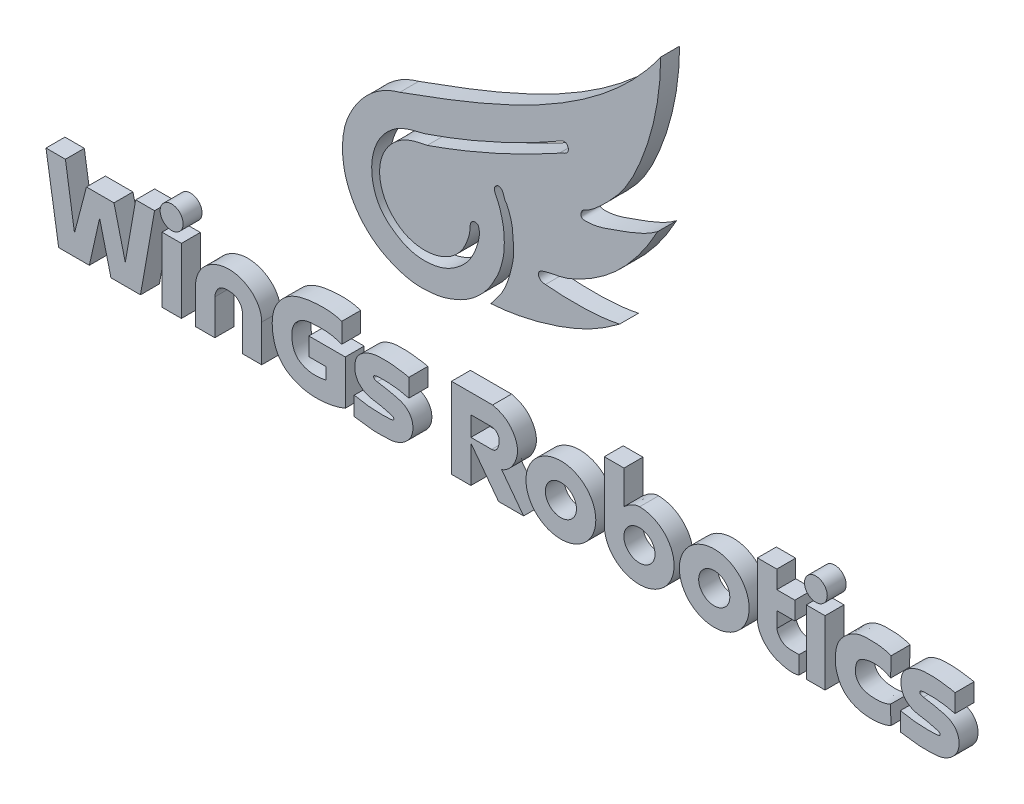
SolidWorks part; units mm, degrees
ref_plane "前视基准面" through (0, 0, 0) normal (0, 0, 1) x (1, 0, 0)
ref_plane "上视基准面" through (0, 0, 0) normal (0, 1, 0) x (1, 0, 0)
ref_plane "右视基准面" through (0, 0, 0) normal (1, 0, 0) x (0, 0, -1)
other "Configuration Table"
sketch "Sketch1" plane through (0, 0, 0) normal (0, 0, 1) x (1, 0, 0)
  line L1 (0, 0) -> (116, 0)
  line L2 (0, 0) -> (0, 86)
  line L3 (0, 86) -> (116, 86)
  line L4 (116, 0) -> (116, 86)
  dimension "D1" = 116
  dimension "D2" = 86
extrude "Boss-Extrude1" add sketch "Sketch1" along normal blind 2
sketch "Sketch2" plane through (0, 0, 2) normal (0, 0, 1) x (1, 0, 0)
  line L0 (9.8027, 28.235) -> (11.8527, 28.235)
  line L1 (11.8527, 28.235) -> (12.8123, 21.9684)
  line L2 (12.8123, 21.9684) -> (14.0773, 26.8101)
  line L3 (14.0773, 26.8101) -> (16.9852, 26.8101)
  line L4 (16.9852, 26.8101) -> (18.1775, 21.9684)
  line L5 (18.1775, 21.9684) -> (19.2825, 28.235)
  line L6 (19.2825, 28.235) -> (21.2744, 28.235)
  line L7 (21.2744, 28.235) -> (19.7853, 19.7903)
  line L8 (19.7853, 19.7903) -> (16.6653, 19.7903)
  line L9 (16.6653, 19.7903) -> (15.4678, 24.6536)
  line L10 (15.4678, 24.6536) -> (14.3826, 19.7903)
  line L11 (14.3826, 19.7903) -> (11.1403, 19.7903)
  line L12 (11.1403, 19.7903) -> (9.8027, 28.235)
  line L13 (22.0595, 26.6647) -> (24.1096, 26.6647)
  line L14 (24.1096, 26.6647) -> (24.1096, 19.7903)
  line L15 (24.1096, 19.7903) -> (22.0595, 19.7903)
  line L16 (22.0595, 19.7903) -> (22.0595, 26.6647)
  line L17 (32.5933, 23.6986) -> (32.5933, 19.7903)
  line L18 (32.5933, 19.7903) -> (30.5505, 19.7903)
  line L19 (30.5505, 19.7903) -> (30.5505, 23.5343)
  line L20 (27.6427, 23.5343) -> (27.6427, 19.7903)
  line L21 (27.6427, 19.7903) -> (25.5972, 19.7903)
  line L22 (25.5972, 19.7903) -> (25.5972, 23.6986)
  line L23 (41.4245, 20.2317) -> (41.4245, 24.9256)
  line L24 (41.4245, 24.9256) -> (37.5759, 24.9256)
  line L25 (37.5759, 24.9256) -> (37.5759, 23.026)
  line L26 (37.5759, 23.026) -> (39.3929, 23.026)
  line L27 (39.3929, 23.026) -> (39.3929, 21.7872)
  line L28 (41.0585, 28.009) -> (41.0585, 25.9029)
  line L29 (42.3726, 19.9426) -> (42.3726, 21.9041)
  line L30 (48.1482, 26.4281) -> (48.1482, 24.5174)
  line L31 (57.9509, 22.8769) -> (60.2681, 19.7995)
  line L32 (60.2681, 19.7995) -> (57.6234, 19.7995)
  line L33 (57.6234, 19.7995) -> (54.6991, 23.6831)
  line L34 (54.6991, 23.6831) -> (54.6991, 19.7995)
  line L35 (54.6991, 19.7995) -> (52.65, 19.7995)
  line L36 (52.65, 19.7995) -> (52.65, 28.3165)
  line L37 (52.65, 28.3165) -> (56.9933, 28.3165)
  line L38 (56.8114, 26.2746) -> (54.6991, 26.2746)
  line L39 (54.6991, 26.2746) -> (54.6991, 24.2045)
  line L40 (54.6991, 24.2045) -> (56.8948, 24.2045)
  line L41 (68.7934, 29.486) -> (70.8757, 29.486)
  line L42 (70.8757, 29.486) -> (70.8757, 25.9572)
  line L43 (68.7934, 29.486) -> (68.8194, 23.6311)
  line L44 (84.9748, 28.3165) -> (87.0193, 28.3165)
  line L45 (87.0193, 28.3165) -> (87.0193, 26.4281)
  line L46 (87.0193, 26.4281) -> (88.9274, 26.4281)
  line L47 (88.9274, 26.4281) -> (88.9274, 24.5174)
  line L48 (88.9274, 24.5174) -> (87.0193, 24.5174)
  line L49 (87.0193, 24.5174) -> (87.0193, 22.8769)
  line L50 (84.9748, 28.3165) -> (84.9748, 22.8769)
  line L51 (89.3697, 19.7903) -> (89.3697, 21.6564)
  line L52 (90.1423, 26.5997) -> (92.1233, 26.5997)
  line L53 (92.1233, 26.5997) -> (92.1233, 19.7903)
  line L54 (92.1233, 19.7903) -> (90.1423, 19.7903)
  line L55 (90.1423, 19.7903) -> (90.1423, 26.5997)
  line L56 (100.0817, 19.9352) -> (100.0817, 21.8967)
  line L57 (105.8573, 26.4207) -> (105.8573, 24.51)
  line L59 (0, 86) -> (116, 86)
  line L60 (0, 86) -> (0, 0)
  line L61 (0, 0) -> (116, 0)
  line L62 (116, 86) -> (116, 0)
  circle A0 centre (23.0773, 28.5403) radius 1.2139
  circle A1 centre (91.149, 28.5403) radius 1.2042
  ellipse E0 centre (64.2087, 23.2238) end of major axis (62.5755, 23.026) minor radius 1.6135
  ellipse E1 centre (64.2087, 23.2238) end of major axis (60.5207, 23.2238) minor radius 3.5863
  ellipse E2 centre (72.5089, 23.2351) end of major axis (70.8757, 23.0374) minor radius 1.6135
  ellipse E3 centre (72.4814, 23.2061) end of major axis (68.7937, 23.2519) minor radius 3.5627 (68.8194, 23.6311) -> (72.4501, 26.7688) ccw
  ellipse E4 centre (80.4111, 23.2582) end of major axis (78.7779, 23.0604) minor radius 1.6135
  ellipse E5 centre (80.4111, 23.2582) end of major axis (76.723, 23.2582) minor radius 3.5863
  spline S0 degree 3 poles (47.1831, 52.0268) (57.216, 55.6604) (68.3491, 59.9142) (74.7524, 69.0372) knots 0 0 0 0 1 1 1 1
  spline S1 degree 3 poles (74.7524, 69.0372) (74.7365, 65.3659) (73.7278, 60.4257) (70.9663, 54.8142) (68.7581, 52.5438) (67.3008, 51.2594) (66.3857, 50.8892) (66.1919, 50.0322) (67.3405, 50.0519) (68.5807, 50.2825) (71.1429, 51.2424) (73.2135, 51.9772) (74.4343, 52.9034) knots 0 0 0 0 0.360634 0.500005 0.614902 0.674582 0.691796 0.711227 0.738156 0.775636 0.851126 1 1 1 1
  spline S2 degree 3 poles (74.4343, 52.9034) (73.5344, 51.2446) (71.9363, 48.8706) (69.1717, 46.2263) (66.8129, 44.6852) (64.459, 43.5637) (62.7709, 43.442) (61.8385, 43.0103) (61.7928, 42.333) (62.306, 42.118) (62.5755, 42.1345) knots 0 0 0 0 0.317486 0.47747 0.639062 0.792073 0.904921 0.928219 0.95201 1 1 1 1
  spline S3 degree 3 poles (62.5755, 42.1345) (63.3547, 42.0538) (64.7001, 41.9914) (66.7084, 41.981) (68.5463, 42.1026) (69.8092, 42.2942) (70.4107, 42.4227) knots 0 0 0 0 0.298501 0.513418 0.765548 1 1 1 1
  spline S4 degree 3 poles (70.4107, 42.4227) (69.0722, 41.3928) (66.6735, 39.9566) (63.1137, 38.6779) (60.0189, 37.8594) (57.9209, 37.5758) (56.8114, 37.504) knots 0 0 0 0 0.345509 0.567874 0.772357 1 1 1 1
  spline S5 degree 3 poles (56.8114, 37.504) (57.1501, 38.014) (57.9873, 38.9045) (58.6132, 40.423) (59.0127, 41.8409) (59.2903, 43.2209) (59.1608, 44.4082) (59.1125, 45.8858) (58.7734, 46.8278) (58.4542, 47.5164) knots 0 0 0 0 0.171911 0.337536 0.453261 0.586014 0.727877 0.785411 1 1 1 1
  spline S6 degree 3 poles (58.4542, 47.5164) (58.1552, 47.7663) (58.2426, 48.4056) (57.6344, 48.7258) (57.3395, 48.5611) (57.1481, 48.3317) (57.1918, 47.9689) (57.3731, 47.5948) (57.6463, 47.0478) (57.8358, 46.4382) (58.0549, 45.6679) (58.1832, 44.9046) (58.2458, 43.8518) (58.2148, 42.7406) (57.9317, 41.5832) (57.6308, 40.6253) (57.1596, 39.7594) (56.5162, 38.6016) (55.4247, 37.4363) (54.1168, 36.4637) (52.8944, 35.9233) (51.7724, 35.5143) (50.4508, 35.3174) (48.7837, 35.2372) (46.8987, 35.6969) (44.9241, 36.6174) (43.1617, 38.1067) (42.0038, 39.9015) (41.341, 41.702) (41.0315, 43.7959) (41.2416, 46.0312) (42.3532, 48.424) (44.0891, 50.6501) (46.0639, 51.7314) (47.1831, 52.0268) knots 0 0 0 0 0.025484 0.033383 0.040232 0.046589 0.052344 0.063459 0.074884 0.093534 0.10647 0.129018 0.145625 0.17776 0.203591 0.22594 0.245355 0.270053 0.315285 0.351906 0.379455 0.405318 0.432327 0.469429 0.51742 0.561659 0.615846 0.670887 0.704018 0.744828 0.813277 0.85164 0.92215 1 1 1 1
  spline S7 degree 3 poles (64.3499, 56.1614) (64.4693, 56.198) (64.7382, 56.2478) (64.9298, 55.9871) (65.0268, 55.728) (64.8911, 55.1487) (64.274, 55.0547) (64.0386, 54.8823) knots 0 0 0 0 0.180535 0.288784 0.393192 0.542414 1 1 1 1
  spline S8 degree 3 poles (64.0386, 54.8823) (59.572, 52.4062) (54.9001, 50.2948) (50.0745, 48.6121) knots 0 0 0 0 1 1 1 1
  spline S9 degree 2 poles (64.3499, 56.1614) (57.4385, 52.1577) (49.8143, 49.5487) knots 0 0 0 1 1 1
  spline S10 degree 3 poles (49.8143, 49.5487) (49.1643, 49.3784) (48.2124, 49.1961) (46.3723, 48.3773) (44.2192, 46.161) (43.9774, 42.6043) (45.2254, 40.0525) (46.5951, 38.9146) (48.299, 37.9908) (50.179, 37.8379) (52.0127, 38.232) (53.3955, 39.1002) (54.5017, 40.1892) (55.1879, 41.4828) (55.5621, 42.6798) (55.6315, 43.5768) (55.4539, 44.1289) (55.208, 44.1161) knots 0 0 0 0 0.074167 0.1054 0.220595 0.394008 0.454413 0.527731 0.585289 0.665338 0.728528 0.788515 0.842168 0.897128 0.948286 0.97672 1 1 1 1
  spline S11 degree 3 poles (55.208, 44.1161) (55.0226, 44.1791) (54.667, 43.959) (54.6094, 43.4642) (54.5978, 42.8636) (54.3423, 42.0093) (53.7764, 40.7342) (52.3297, 39.3376) (50.1524, 38.7214) (47.7052, 39.1332) (45.9303, 40.6216) (44.9775, 42.794) (45.0428, 45.5373) (47.1244, 48.0082) (49.206, 48.4687) (50.0745, 48.6121) knots 0 0 0 0 0.023493 0.044042 0.061062 0.101136 0.156797 0.23921 0.350066 0.433771 0.549578 0.629423 0.732521 0.886291 1 1 1 1
  spline S12 degree 3 poles (25.5972, 23.6986) (25.655, 24.3658) (26.0941, 25.5117) (27.5424, 26.5737) (30.2768, 27.2067) (32.5736, 25.5619) (32.5933, 23.6986) knots 0 0 0 0 0.198571 0.34064 0.5135 1 1 1 1
  spline S13 degree 3 poles (30.5505, 23.5343) (30.5434, 23.9759) (30.1068, 24.7165) (29.076, 24.8585) (28.0074, 24.7723) (27.6729, 23.9331) (27.6427, 23.5343) knots 0 0 0 0 0.311205 0.495488 0.702071 1 1 1 1
  spline S14 degree 3 poles (41.0585, 28.009) (40.0534, 28.3395) (38.2528, 28.3483) (35.58, 27.8618) (33.8071, 26.0118) (33.5909, 23.4895) (34.2599, 21.0828) (36.5954, 19.6795) (39.0686, 19.544) (40.7235, 19.9364) (41.4245, 20.2317) knots 0 0 0 0 0.156695 0.267521 0.399378 0.502862 0.637623 0.747872 0.886035 1 1 1 1
  spline S15 degree 3 poles (39.3929, 21.7872) (38.7093, 21.6487) (37.5769, 21.5423) (36.1025, 22.3452) (35.7049, 23.7435) (35.8131, 25.2008) (36.9698, 26.204) (38.2345, 26.2733) (39.6234, 26.3182) (40.5236, 26.0878) (41.0585, 25.9029) knots 0 0 0 0 0.181467 0.284135 0.402884 0.534993 0.639881 0.765013 0.852735 1 1 1 1
  spline S16 degree 2 poles (48.1482, 24.5174) (46.544, 24.9457) (44.8888, 24.8527) knots 0 0 0 1 1 1
  spline S17 degree 2 poles (44.8888, 24.8527) (44.6892, 24.8488) (44.5108, 24.7528) knots 0 0 0 1 1 1
  spline S18 degree 3 poles (44.5108, 24.7528) (44.4063, 24.7177) (44.3879, 24.4124) (44.7022, 24.3838) (44.8061, 24.3456) knots 0 0 0 0 0.400794 1 1 1 1
  spline S19 degree 3 poles (44.8061, 24.3456) (45.4236, 24.274) (46.288, 24.0648) (47.4629, 23.8067) (48.147, 23.319) (48.5456, 22.5902) (48.6196, 21.7633) (48.3197, 20.8064) (47.5722, 20.1396) (46.6088, 19.7108) (45.569, 19.6812) (44.1213, 19.6404) (43.0613, 19.8702) (42.3726, 19.9426) knots 0 0 0 0 0.150366 0.217158 0.290606 0.346071 0.414261 0.48693 0.581715 0.647373 0.740089 0.830727 1 1 1 1
  spline S20 degree 3 poles (42.3726, 21.9041) (42.8525, 21.8037) (43.5405, 21.6847) (44.4782, 21.597) (45.1945, 21.5883) (45.8688, 21.5828) (46.3005, 21.6313) (46.5297, 21.6877) (46.5567, 21.797) (46.5523, 21.9643) (46.379, 22.021) (46.3173, 22.049) knots 0 0 0 0 0.315552 0.449833 0.605449 0.778844 0.876435 0.89782 0.91722 0.942476 1 1 1 1
  spline S21 degree 3 poles (46.3173, 22.049) (45.8247, 22.2107) (44.9758, 22.4016) (43.6481, 22.557) (42.7017, 23.2519) (42.4205, 24.1635) (42.4311, 24.8543) (42.5725, 25.4907) (43.0041, 26.0044) (43.5079, 26.3588) (44.1094, 26.601) (44.7443, 26.7343) (45.4456, 26.7433) (46.2623, 26.7426) (47.164, 26.593) (47.8325, 26.5196) (48.1482, 26.4281) knots 0 0 0 0 0.129354 0.21684 0.332807 0.395282 0.447956 0.504879 0.55359 0.611568 0.6573 0.714661 0.772387 0.8321 0.918346 1 1 1 1
  spline S22 degree 3 poles (56.9933, 28.3165) (57.5079, 28.1999) (58.406, 27.8613) (59.3049, 26.8025) (59.7648, 25.5393) (59.3451, 23.9707) (58.5781, 23.1135) (57.9509, 22.8769) knots 0 0 0 0 0.216647 0.372499 0.551297 0.738033 1 1 1 1
  spline S23 degree 3 poles (56.8114, 26.2746) (57.1651, 26.312) (57.7627, 25.8573) (57.663, 24.8197) (57.3325, 24.1932) (56.8948, 24.2045) knots 0 0 0 0 0.345185 0.626261 1 1 1 1
  spline S24 degree 3 poles (70.8757, 25.9572) (71.1665, 26.2093) (71.6761, 26.5782) (72.2834, 26.7779) (72.5256, 26.7686) knots 0 0 0 0 0.616176 1 1 1 1
  spline S25 degree 3 poles (84.9748, 22.8769) (84.9049, 21.5816) (85.8804, 20.4707) (87.0193, 20.0095) knots 0 0 0 0 1 1 1 1
  spline S26 degree 3 poles (87.0193, 20.0095) (87.7648, 19.7661) (88.5925, 19.5177) (89.3697, 19.7903) knots 0 0 0 0 1 1 1 1
  spline S27 degree 3 poles (89.3697, 21.6564) (88.8864, 21.6815) (88.1032, 21.5524) (87.2817, 22.1652) (87.0872, 22.6179) (87.0193, 22.8769) knots 0 0 0 0 0.51466 0.724878 1 1 1 1
  spline S28 degree 1 poles (99.1074, 26.4281) (99.0451, 24.3456) knots 0 0 1 1
  spline S29 degree 1 poles (99.0451, 21.9684) (99.0762, 20.0095) knots 0 0 1 1
  spline S30 degree 3 poles (99.0451, 24.3456) (98.1408, 24.9177) (96.9334, 25.0104) (95.9622, 24.5174) knots 0 0 0 0 1 1 1 1
  spline S31 degree 3 poles (95.9622, 24.5174) (95.5905, 24.3596) (95.3714, 23.8067) (95.285, 23.0241) (95.4658, 22.3958) (95.9075, 21.9602) (96.4713, 21.7289) (97.5261, 21.5847) (98.4341, 21.6572) (99.0451, 21.9684) knots 0 0 0 0 0.178932 0.272004 0.383259 0.483726 0.563109 0.676721 1 1 1 1
  spline S32 degree 3 poles (99.1074, 26.4281) (98.7068, 26.5706) (98.0571, 26.739) (97.1441, 26.7697) (96.4259, 26.789) (95.6235, 26.6801) (94.7667, 26.291) (94.0187, 25.6423) (93.3941, 24.7521) (93.1988, 23.7089) (93.1885, 22.6621) (93.4504, 21.6401) (94.6922, 19.4323) (97.6705, 19.3697) (99.0762, 20.0095) knots 0 0 0 0 0.080032 0.124598 0.171299 0.214887 0.2755 0.344981 0.398822 0.476451 0.539473 0.594477 0.673245 1 1 1 1
  spline S33 degree 2 poles (105.8573, 24.51) (104.2531, 24.9383) (102.5979, 24.8453) knots 0 0 0 1 1 1
  spline S34 degree 2 poles (102.5979, 24.8453) (102.3983, 24.8414) (102.2199, 24.7454) knots 0 0 0 1 1 1
  spline S35 degree 3 poles (102.2199, 24.7454) (102.1154, 24.7103) (102.097, 24.405) (102.4113, 24.3764) (102.5152, 24.3382) knots 0 0 0 0 0.400794 1 1 1 1
  spline S36 degree 3 poles (102.5152, 24.3382) (103.1327, 24.2666) (103.9971, 24.0574) (105.172, 23.7993) (105.8561, 23.3116) (106.2547, 22.5828) (106.3287, 21.7559) (106.0288, 20.799) (105.2813, 20.1322) (104.3179, 19.7034) (103.2781, 19.6738) (101.8304, 19.633) (100.7704, 19.8627) (100.0817, 19.9352) knots 0 0 0 0 0.150366 0.217158 0.290606 0.346071 0.414261 0.48693 0.581715 0.647373 0.740089 0.830727 1 1 1 1
  spline S37 degree 3 poles (100.0817, 21.8967) (100.5616, 21.7963) (101.2496, 21.6773) (102.1873, 21.5896) (102.9036, 21.5809) (103.5779, 21.5754) (104.0096, 21.6239) (104.2387, 21.6803) (104.2658, 21.7896) (104.2614, 21.9568) (104.0881, 22.0136) (104.0264, 22.0416) knots 0 0 0 0 0.315552 0.449833 0.605449 0.778844 0.876435 0.89782 0.91722 0.942476 1 1 1 1
  spline S38 degree 3 poles (104.0264, 22.0416) (103.5338, 22.2033) (102.6849, 22.3942) (101.3572, 22.5496) (100.4108, 23.2445) (100.1296, 24.1561) (100.1402, 24.8468) (100.2816, 25.4833) (100.7132, 25.997) (101.217, 26.3514) (101.8185, 26.5936) (102.4534, 26.7269) (103.1547, 26.7359) (103.9714, 26.7352) (104.8731, 26.5856) (105.5416, 26.5122) (105.8573, 26.4207) knots 0 0 0 0 0.129354 0.21684 0.332807 0.395282 0.447956 0.504879 0.55359 0.611568 0.6573 0.714661 0.772387 0.8321 0.918346 1 1 1 1
  line M91 (0, 86) -> (0, 0)
  line M92 (0, 0) -> (116, 0)
  line M93 (116, 0) -> (116, 86)
  line M94 (116, 86) -> (0, 86)
extrude "Cut-Extrude2" cut sketch "Sketch2" against normal blind 11 contours S32 S28 S30 S31 S29 S27 L51 S26 S25 L50 L44 L45 L46 L47 L48 L49 L37 S22 L31 L32 L33 L34 L35 L36 S15 L27 L26 L25 L24 L23 S14 L28 E5 E1 A1 A0 L11 L12 M94 M91 M92 M93 | S10 S11 S8 S7 S9 | S23 L38 L39 L40 | E0 | E2 | E4
